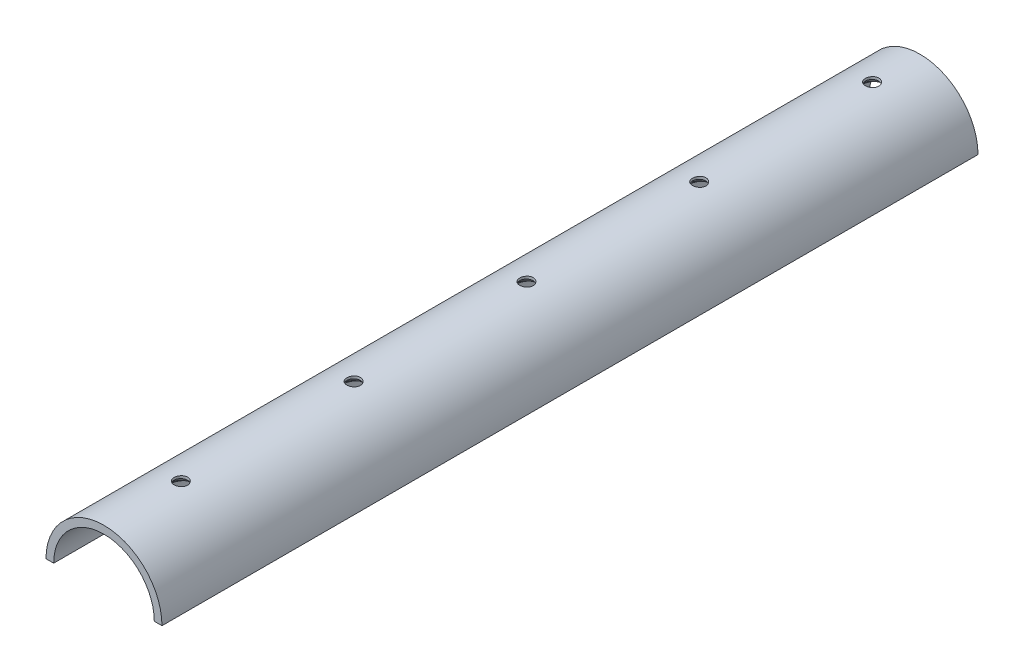
SolidWorks part; units mm, degrees
ref_plane "Front Plane" through (0, 0, 0) normal (0, 0, 1) x (1, 0, 0)
ref_plane "Top Plane" through (0, 0, 0) normal (0, 1, 0) x (1, 0, 0)
ref_plane "Right Plane" through (0, 0, 0) normal (1, 0, 0) x (0, 0, -1)
sketch "Sketch2" plane through (0, 0, 0) normal (0, 0, 1) x (1, 0, 0)
  circle A0 centre (0, 0) radius 30.2
  dimension "D1" = 60.4
extrude "Boss-Extrude1" add sketch "Sketch2" against normal blind 425
sketch "Sketch3" plane through (0, 0, 0) normal (0, 0, 1) x (1, 0, 0)
  circle A0 centre (0, 0) radius 26.2
  circle A1 centre (0, 0) radius 30.2 construction
  dimension "D1" = 4
extrude "Cut-Extrude1" cut sketch "Sketch3" against normal through all
sketch "Sketch4" plane through (0, 0, 0) normal (0, 1, 0) x (1, 0, 0)
  line L1 (-30.2, 425) -> (30.2, 425)
  line L2 (-30.2, 425) -> (-30.2, 0)
  line L3 (-30.2, 0) -> (30.2, 0)
  line L4 (30.2, 425) -> (30.2, 0)
extrude "Cut-Extrude2" cut sketch "Sketch4" against normal up to next
sketch "Sketch5" plane through (0, 0, 0) normal (0, 1, 0) x (1, 0, 0)
  line L0 (0, 40) -> (0, 130) construction
  point P0 (0, 40)
  point P1 (0, 400)
  point P4 (0, 130)
  point P7 (0, 220)
  point P8 (0, 310)
  dimension "D1" = 40
  dimension "D2" = 90
  dimension "D3" = 5
hole_wizard "CSK for M6 Flat Head Machine Screw1" positions "Sketch9" profile "Sketch10" countersink size "M6" standard "ANSI Metric" end condition through all
sketch "Sketch9" plane through (0, 0, 0) normal (0, -1, 0) x (-1, 0, 0)
  point P45 (0, 40)
  point P48 (0, 130)
  point P51 (0, 220)
  point P54 (0, 310)
  point P57 (0, 400)
sketch "Sketch10" plane through (0, 0, -40) normal (1, 0, 0) x (0, 0, -1)
  line L0 (0, 0) -> (0, 30.2)
  line L1 (0, 30.2) -> (3.5, 30.2)
  line L2 (3.5, 30.2) -> (3.5, 28.8)
  line L3 (3.5, 28.8) -> (6.3, 26)
  line L4 (6.3, 26) -> (6.3, 0)
  line L6 (6.3, 0) -> (0, 0)
  line L7 (-3.5, 28.8) -> (-6.3, 26) construction
  line L11 (0, -6.35) -> (0, 107.95) construction
  dimension "Thru Hole Dia." = 7
  dimension "Thru Hole Depth" = 30.2
  dimension "C'Sink Dia." = 12.6
  dimension "C'Sink Angle" = 90
  dimension "Head Clearance" = 26
